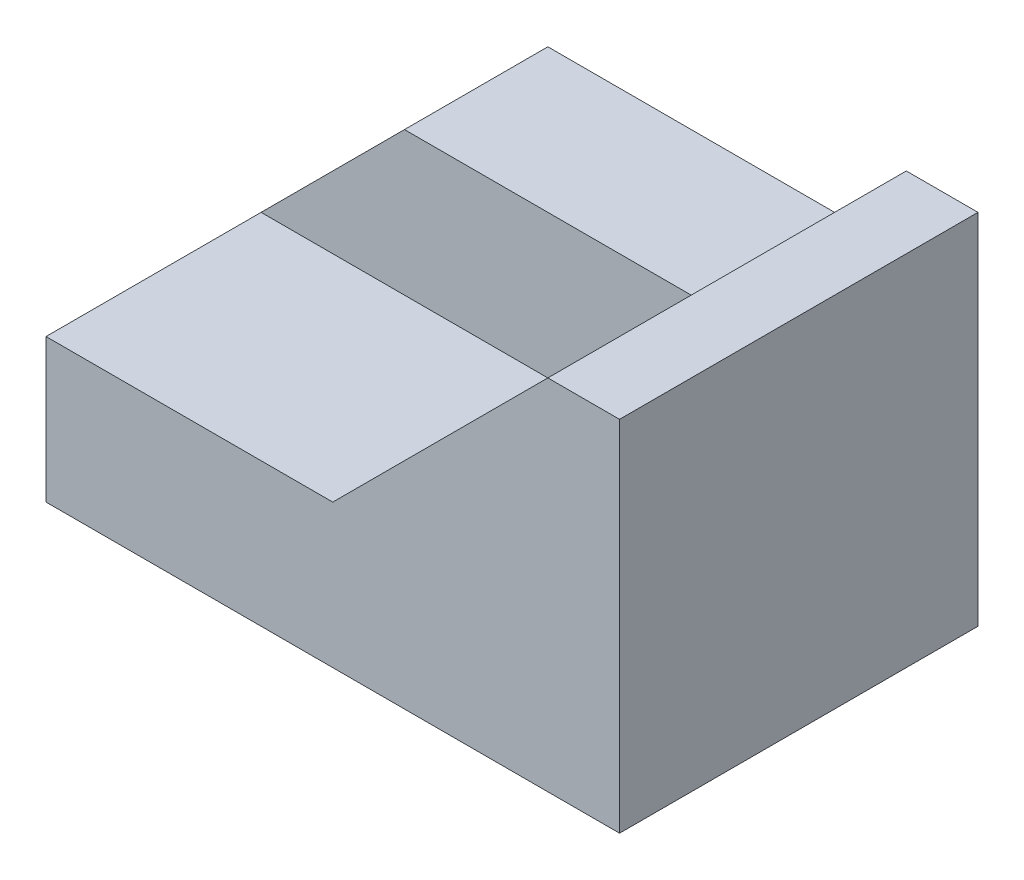
SolidWorks part; units mm, degrees
ref_plane "Front Plane" through (0, 0, 0) normal (0, 0, 1) x (1, 0, 0)
ref_plane "Top Plane" through (0, 0, 0) normal (0, 1, 0) x (1, 0, 0)
ref_plane "Right Plane" through (0, 0, 0) normal (1, 0, 0) x (0, 0, -1)
sketch "Sketch1" plane through (0, 0, 0) normal (0, 0, 1) x (1, 0, 0)
  line L1 (0, 0) -> (80, 0)
  line L2 (0, 0) -> (0, 50)
  line L3 (0, 50) -> (80, 50)
  line L4 (80, 0) -> (80, 50)
  dimension "D1" = 80
  dimension "D2" = 50
extrude "Boss-Extrude1" add sketch "Sketch1" along normal blind 50
sketch "Sketch2" plane through (0, 0, 50) normal (0, 0, 1) x (1, 0, 0)
  line L0 (70, 50) -> (60, 40)
  line L1 (80, 50) -> (0, 50) construction
  line L2 (60, 40) -> (20, 40)
  line L3 (20, 40) -> (0, 20)
  line L4 (0, 50) -> (0, 0) construction
  line L5 (0, 20) -> (0, 50)
  line L6 (0, 50) -> (70, 50)
  dimension "D1" = 10
  dimension "D2" = 10
  dimension "D3" = 10
  dimension "D4" = 40
  dimension "D5" = 20
extrude "Cut-Extrude1" cut sketch "Sketch2" against normal blind 50
sketch "Sketch3" plane through (0, 0, 50) normal (0, 0, 1) x (1, 0, 0)
  line L0 (0, 20) -> (40, 20)
  line L1 (40, 20) -> (60, 40)
  line L2 (60, 40) -> (20, 40)
  line L3 (20, 40) -> (0, 20)
  dimension "D1" = 40
extrude "Cut-Extrude2" cut sketch "Sketch3" against normal blind 30
